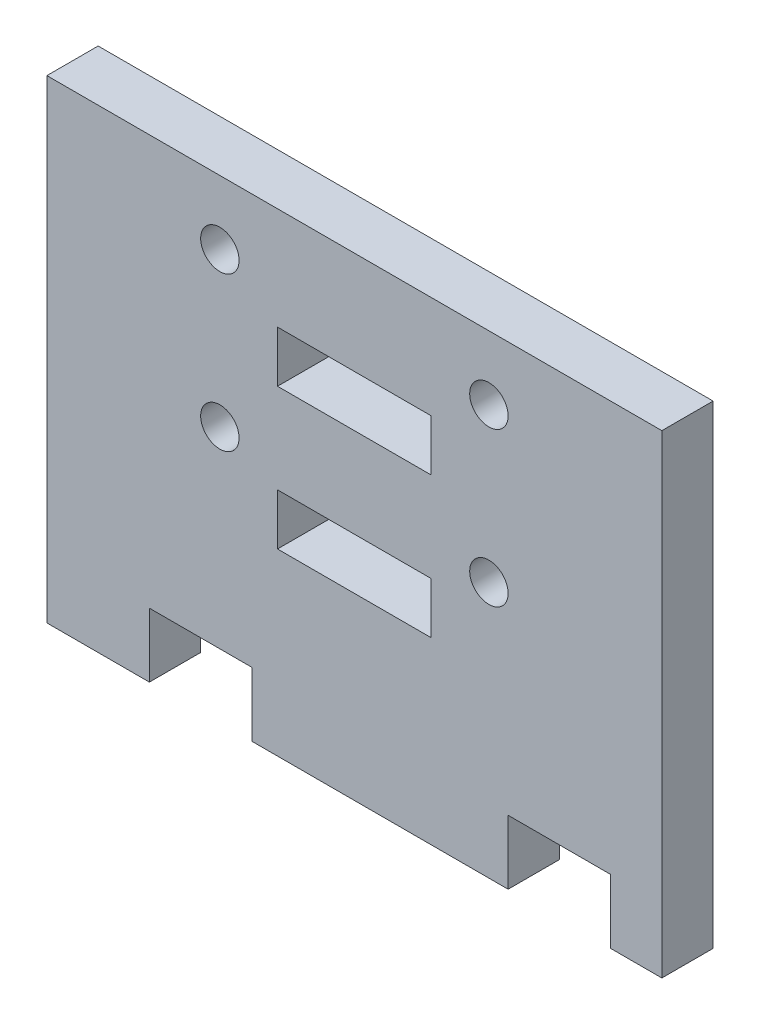
SolidWorks part; units mm, degrees
ref_plane "Front Plane" through (0, 0, 0) normal (0, 0, 1) x (1, 0, 0)
ref_plane "Top Plane" through (0, 0, 0) normal (0, 1, 0) x (1, 0, 0)
ref_plane "Right Plane" through (0, 0, 0) normal (1, 0, 0) x (0, 0, -1)
sketch "Sketch1" plane through (0, 0, 0) normal (0, 0, 1) x (1, 0, 0)
  line L0 (4, 2.5) -> (8, 2.5)
  line L1 (4, 0) -> (0, 0)
  line L2 (0, 18.5) -> (24, 18.5)
  line L3 (0, 0) -> (0, 18.5)
  line L4 (9, 14.5) -> (9, 12.5)
  line L5 (15, 14.5) -> (9, 14.5)
  line L6 (9, 12.5) -> (15, 12.5)
  line L7 (15, 12.5) -> (15, 14.5)
  line L8 (4, 2.5) -> (4, 0)
  line L9 (22, 0) -> (24, 0)
  line L10 (24, 0) -> (24, 18.5)
  line L11 (18, 0) -> (18, 2.5)
  line L12 (15, 7) -> (15, 9)
  line L13 (9, 7) -> (15, 7)
  line L14 (22, 2.5) -> (22, 0)
  line L15 (15, 9) -> (9, 9)
  line L16 (9, 9) -> (9, 7)
  line L17 (18, 2.5) -> (22, 2.5)
  line L18 (8, 0) -> (8, 2.5)
  line L19 (8, 0) -> (18, 0)
  circle A0 centre (6.75, 16) radius 0.75
  circle A1 centre (17.25, 16) radius 0.75
  circle A2 centre (17.25, 10) radius 0.75
  circle A3 centre (6.75, 10) radius 0.75
  dimension "D2" = 4
  dimension "D3" = 4
  dimension "D4" = 10
  dimension "D5" = 4
  dimension "D1" = 18.5
  dimension "D6" = 2
  dimension "D18" = 2.25
  dimension "D22" = 1.5
  dimension "D23" = 2.25
  dimension "D7" = 2.5
  dimension "D8" = 2.5
  dimension "D9" = 24
  dimension "D10" = 2.5
  dimension "D11" = 2.5
  dimension "D12" = 7
  dimension "D13" = 9
  dimension "D14" = 6
  dimension "D15" = 2
  dimension "D16" = 12.5
  dimension "D17" = 9
  dimension "D19" = 6
  dimension "D21" = 2.25
  dimension "D24" = 1
  dimension "D25" = 1.5
  dimension "D26" = 1.5
  dimension "D27" = 1
extrude "Boss-Extrude1" add sketch "Sketch1" along normal blind 2
equation "\"D18@Sketch1\"= \"fingerWidth@parametersSketch@prostheticParameters.SLDPRT\" - 13.95 'Distance hole 1 Base thumb"
equation "\"D21@Sketch1\"= \"fingerWidth@parametersSketch@prostheticParameters.SLDPRT\" - 13.95 'Distance hole 3 Base thumb"
equation "\"D23@Sketch1\"= \"fingerWidth@parametersSketch@prostheticParameters.SLDPRT\" - 13.95 'Distance hole 4 Base thumb"
